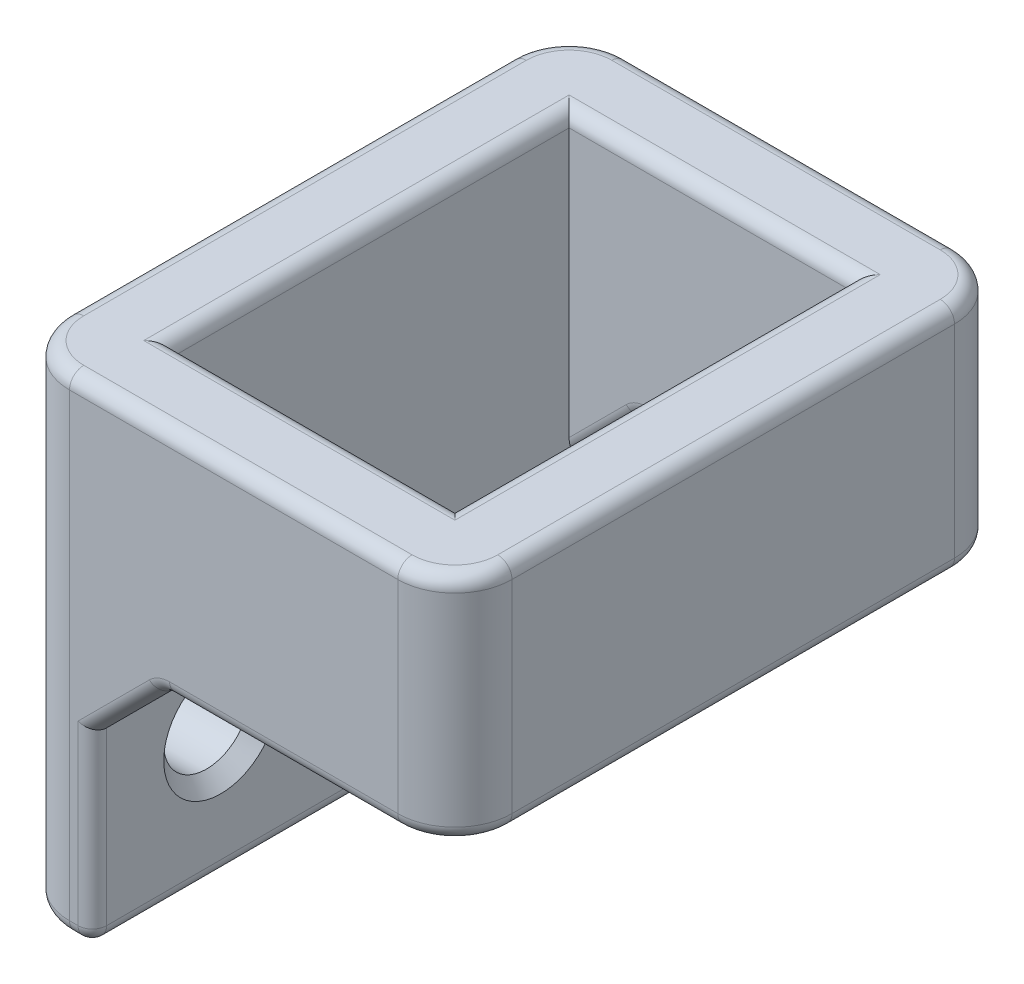
SolidWorks part; units mm, degrees
ref_plane "Plano frontal" through (0, 0, 0) normal (0, 0, 1) x (1, 0, 0)
ref_plane "Plano superior" through (0, 0, 0) normal (0, 1, 0) x (1, 0, 0)
ref_plane "Plano direito" through (0, 0, 0) normal (1, 0, 0) x (0, 0, -1)
sketch "Sketch1" plane through (0, 0, 0) normal (0, 1, 0) x (1, 0, 0)
  line L0 (-7.75, 9.75) -> (7.75, 9.75)
  line L5 (-4.75, 6.75) -> (4.75, 6.75) construction
  line L6 (-4.75, 6.75) -> (-4.75, -6.75) construction
  line L7 (-4.75, -6.75) -> (4.75, -6.75) construction
  line L8 (4.75, 6.75) -> (4.75, -6.75) construction
  line L9 (7.75, 9.75) -> (7.75, -9.75)
  line L10 (-7.75, -9.75) -> (7.75, -9.75)
  line L11 (-7.75, 9.75) -> (-7.75, -9.75)
  line L12 (-4.95, 6.95) -> (4.95, 6.95)
  line L13 (4.95, 6.95) -> (4.95, -6.95)
  line L14 (-4.95, -6.95) -> (4.95, -6.95)
  line L15 (-4.95, 6.95) -> (-4.95, -6.95)
  point P11 (0, -6.75)
  point P12 (-4.75, 0)
  dimension "D1" = 9.5
  dimension "D2" = 13.5
  dimension "D3" = 3
  dimension "D4" = 0.2
extrude "Boss-Extrude1" add sketch "Sketch1" along normal mid plane 8.1
sketch "Sketch2" plane through (-7.75, 0, 0) normal (-1, 0, 0) x (0, 0, 1)
  line L0 (9.75, 4.05) -> (9.75, -4.05) construction
  line L1 (-9.75, -4.05) -> (9.75, -4.05)
  line L2 (-9.75, -4.05) -> (-9.75, -13.05)
  line L3 (-9.75, -13.05) -> (9.75, -13.05)
  line L4 (9.75, -4.05) -> (9.75, -13.05)
  line L5 (0, -8.525) -> (0, 8.525) construction
  circle A0 centre (-5.25, -8.55) radius 1.5
  circle A2 centre (5.25, -8.55) radius 1.5
  dimension "D1" = 3
  dimension "D2" = 3
  dimension "D3" = 3
  dimension "D4" = 3
extrude "Boss-Extrude2" add sketch "Sketch2" against normal up to surface (2.8 mm away) up to face at (-4.95, 0, 0)
chamfer "Chamfer1" distance 2.5 angle 45 2 edges at (-4.95, -4.05, -8.35) (-4.95, -4.05, 8.35)
fillet "Fillet1" radius 2 4 edges at (-7.75, -4.5, 9.75) (-7.75, -4.5, -9.75) (7.75, 0, -9.75) (7.75, 0, 9.75)
fillet "Fillet2" radius 0.5 34 edges at (-7.1642, -13.05, 9.1642) (-4.95, -13.05, 0) (-7.1642, -13.05, -9.1642) (-7.75, -13.05, 0) (7.1642, -4.05, 9.1642) (7.75, -4.05, 0) (7.1642, -4.05, -9.1642) (-4.95, -9.8, 9.75) (-5.35, -13.05, 9.75) (1.65, -4.05, 9.75) (-5.35, -13.05, -9.75) (-4.95, -9.8, -9.75) (1.65, -4.05, -9.75) (7.1642, 4.05, 9.1642) (0, 4.05, 9.75) (-7.1642, 4.05, 9.1642) (-7.75, 4.05, 0) (-7.1642, 4.05, -9.1642) (0, 4.05, -9.75) (7.1642, 4.05, -9.1642) (7.75, 4.05, 0) (1.25, -4.05, -6.95) (4.95, -4.05, 0) (1.25, -4.05, 6.95) (4.95, 4.05, 0) (0, 4.05, -6.95) (-4.95, 4.05, 0) (0, 4.05, 6.95) (-3.7, -5.3, -6.95) (-3.7, -5.3, 6.95) (-2.45, -4.05, -8.35) (-2.45, -4.05, 8.35) (-3.7, -5.3, 9.75) (-3.7, -5.3, -9.75)
chamfer "Chamfer2" distance 0.5 angle 45 2 edges at (-4.95, -8.55, -6.75) (-4.95, -8.55, 3.75)
